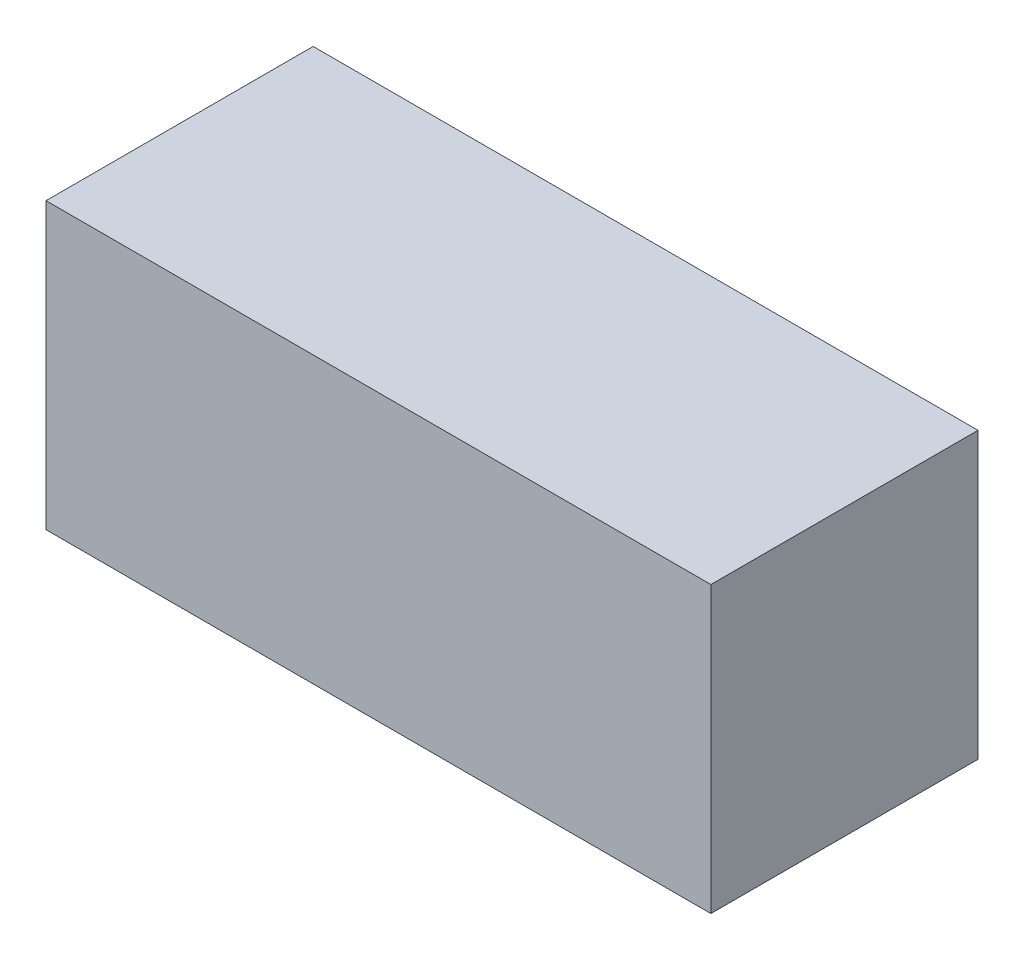
SolidWorks part; units mm, degrees
ref_plane "Front Plane" through (0, 0, 0) normal (0, 0, 1) x (1, 0, 0)
ref_plane "Top Plane" through (0, 0, 0) normal (0, 1, 0) x (1, 0, 0)
ref_plane "Right Plane" through (0, 0, 0) normal (1, 0, 0) x (0, 0, -1)
sketch "Sketch1" plane through (0, 0, 0) normal (0, 1, 0) x (1, 0, 0)
  line L0 (0, 22.5) -> (0, -22.5) construction
  line L1 (-56, 22.5) -> (56, 22.5)
  line L2 (-56, 22.5) -> (-56, -22.5)
  line L3 (-56, -22.5) -> (56, -22.5)
  line L4 (56, 22.5) -> (56, -22.5)
  point P6 (0, 0)
  dimension "D1" = 45
  dimension "D2" = 112
extrude "Boss-Extrude1" add sketch "Sketch1" along normal blind 48
